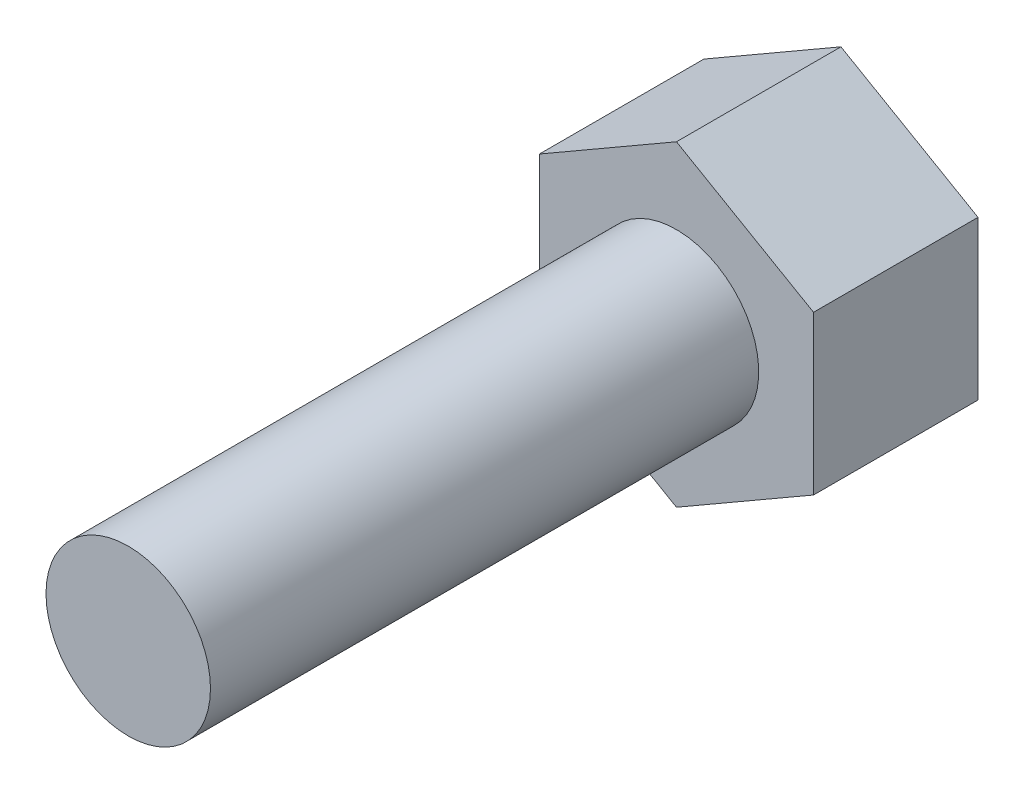
SolidWorks part; units mm, degrees
ref_plane "Front Plane" through (0, 0, 0) normal (0, 0, 1) x (1, 0, 0)
ref_plane "Top Plane" through (0, 0, 0) normal (0, 1, 0) x (1, 0, 0)
ref_plane "Right Plane" through (0, 0, 0) normal (1, 0, 0) x (0, 0, -1)
sketch "Sketch1" plane through (0, 0, 0) normal (0, 0, 1) x (1, 0, 0)
  circle A0 centre (-63.4948, 14.9787) radius 1.5
extrude "Boss-Extrude1" add sketch "Sketch1" along normal blind 10
sketch "Sketch2" plane through (0, 0, 0) normal (0, 0, -1) x (-1, 0, 0)
  line L1 (63.4948, 12.092) -> (65.9948, 13.5353)
  line L2 (65.9948, 13.5353) -> (65.9948, 16.4221)
  line L3 (65.9948, 16.4221) -> (63.4948, 17.8655)
  line L4 (63.4948, 17.8655) -> (60.9948, 16.4221)
  line L5 (60.9948, 16.4221) -> (60.9948, 13.5353)
  line L6 (60.9948, 13.5353) -> (63.4948, 12.092)
  circle A0 centre (63.4948, 14.9787) radius 2.5 construction
  dimension "D1" = 5
extrude "Boss-Extrude2" add sketch "Sketch2" along normal blind 3
